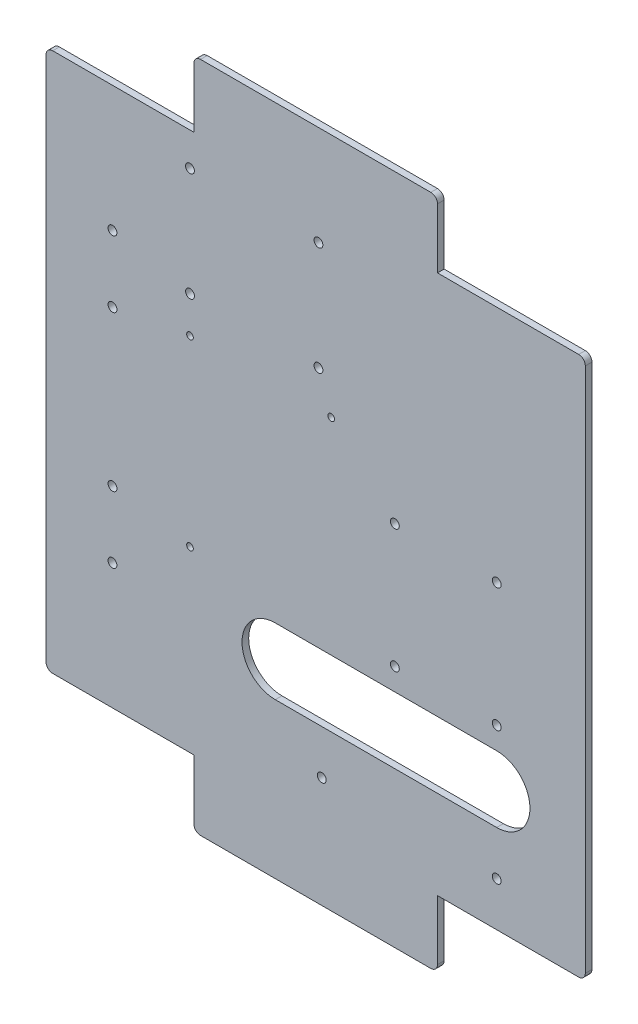
SolidWorks part; units mm, degrees
material "Alliage 1060"
ref_plane "Plan de dessus" through (0, 0, 0) normal (0, 0, 1) x (1, 0, 0)
ref_plane "Plan de droite" through (0, 0, 0) normal (0, 1, 0) x (1, 0, 0)
ref_plane "Plan de face" through (0, 0, 0) normal (1, 0, 0) x (0, 0, -1)
sketch "Esquisse1" plane through (0, 0, 0) normal (0, 0, 1) x (1, 0, 0)
  line L0 (0, 0) -> (-200, 0)
  line L1 (-200, 0) -> (-224.7487, 24.7487)
  line L2 (-224.7487, 24.7487) -> (-224.7487, 284.7487)
  line L3 (-224.7487, 284.7487) -> (-200, 309.4975)
  line L4 (-200, 309.4975) -> (0, 309.4975)
  line L5 (0, 309.4975) -> (24.7487, 284.7487)
  line L6 (24.7487, 284.7487) -> (24.7487, 24.7487)
  line L7 (24.7487, 24.7487) -> (0, 0)
  dimension "D1" = 260
  dimension "D2" = 35
  dimension "D3" = 135
  dimension "D4" = 200
extrude "Base" add sketch "Esquisse1" along normal blind 3
fillet "Congé1" radius 3 8 edges at (-200, 0, 1.5) (-224.7487, 24.7487, 1.5) (-224.7487, 284.7487, 1.5) (-200, 309.4975, 1.5) (0, 309.4975, 1.5) (24.7487, 284.7487, 1.5) (24.7487, 24.7487, 1.5) (0, 0, 1.5)
sketch "Esquisse19" plane through (0, 0, 0) normal (0, 0, -1) x (-1, 0, 0)
  line L0 (100, 309.4975) -> (100, 0) construction
  line L1 (1.2426, 309.4975) -> (198.7574, 309.4975) construction
  line L2 (198.7574, 0) -> (1.2426, 0) construction
  line L3 (-24.7487, 154.7487) -> (224.7487, 154.7487) construction
  line L4 (-24.7487, 25.9914) -> (-24.7487, 283.5061) construction
  line L5 (224.7487, 283.5061) -> (224.7487, 25.9914) construction
sketch "Esquisse25" plane through (0, 0, 0) normal (0, 0, -1) x (-1, 0, 0)
  line L0 (-24.7487, 25.9914) -> (-24.7487, 283.5061) construction
  line L1 (-21.7487, 33) -> (45, 33)
  line L2 (-24.7487, 33) -> (-24.7487, 0)
  line L3 (-24.7487, 0) -> (45, 0)
  line L4 (45, 33) -> (45, 3)
  line L5 (198.7574, 0) -> (1.2426, 0) construction
  line L6 (100, 309.4975) -> (100, 0) construction
  line L7 (100, 0) -> (100, 309.4975) construction
  line L8 (-24.7487, 154.7487) -> (224.7487, 154.7487) construction
  line L9 (224.7487, 0) -> (155, 0)
  line L10 (155, 33) -> (155, 3)
  line L11 (221.7487, 33) -> (155, 33)
  line L12 (224.7487, 33) -> (224.7487, 0)
  line L13 (224.7487, 276.4975) -> (224.7487, 309.4975)
  line L14 (221.7487, 276.4975) -> (155, 276.4975)
  line L15 (155, 276.4975) -> (155, 306.4975)
  line L16 (224.7487, 309.4975) -> (155, 309.4975)
  line L17 (-24.7487, 309.4975) -> (45, 309.4975)
  line L18 (45, 276.4975) -> (45, 306.4975)
  line L19 (-21.7487, 276.4975) -> (45, 276.4975)
  line L20 (-24.7487, 276.4975) -> (-24.7487, 309.4975)
  line L22 (45, 309.4975) -> (155, 309.4975)
  line L24 (45, 306.4975) -> (155, 306.4975)
  line L26 (45, 0) -> (155, 0)
  line L28 (45, 3) -> (155, 3)
  line L31 (-24.7487, 276.4975) -> (-24.7487, 33)
  line L33 (-21.7487, 276.4975) -> (-21.7487, 33)
  line L35 (224.7487, 276.4975) -> (224.7487, 33)
  line L37 (221.7487, 276.4975) -> (221.7487, 33)
  dimension "D1" = 55
  dimension "D2" = 33
  dimension "D3" = 3
  dimension "D4" = 3
  dimension "D5" = 3
  dimension "D6" = 3
extrude "Enlèv. mat.-Extru.1" cut sketch "Esquisse25" against normal through all
fillet "Congé2" radius 3 8 edges at (21.7487, 33, 1.5) (-45, 3, 1.5) (21.7487, 276.4975, 1.5) (-45, 306.4975, 1.5) (-155, 306.4975, 1.5) (-221.7487, 276.4975, 1.5) (-221.7487, 33, 1.5) (-155, 3, 1.5)
sketch "Esquisse26" plane through (0, 0, 0) normal (0, 0, -1) x (-1, 0, 0)
  line L0 (191.7487, 189.7487) -> (191.7487, 219.7487) construction
  line L1 (221.7487, 36) -> (221.7487, 273.4975) construction
  line L2 (-24.7487, 154.7487) -> (224.7487, 154.7487) construction
  line L3 (224.7487, 154.7487) -> (-24.7487, 154.7487) construction
  line L4 (100, 309.4975) -> (100, 0) construction
  circle A0 centre (191.7487, 189.7487) radius 2
  circle A1 centre (191.7487, 219.7487) radius 2
  circle A2 centre (191.7487, 89.7487) radius 2
  circle A3 centre (191.7487, 119.7487) radius 2
  point P8 (191.7487, 204.7487)
  dimension "D1" = 4
  dimension "D2" = 30
  dimension "D3" = 30
  dimension "D4" = 50
extrude "Enlèv. mat.-Extru.2" cut sketch "Esquisse26" against normal through all
sketch "Esquisse27" plane through (0, 0, 0) normal (0, 0, -1) x (-1, 0, 0)
  line L0 (97.2513, 53) -> (18.2513, 53) construction
  line L1 (-21.7487, 273.4975) -> (-21.7487, 36) construction
  line L2 (-18.7487, 33) -> (45, 33) construction
  circle A0 centre (97.2513, 53) radius 2
  circle A1 centre (18.2513, 53) radius 2
  dimension "D2" = 4
  dimension "D1" = 79
  dimension "D3" = 40
  dimension "D4" = 20
extrude "Enlèv. mat.-Extru.3" cut sketch "Esquisse27" against normal through all
sketch "Esquisse28" plane through (0, 0, 0) normal (0, 0, -1) x (-1, 0, 0)
  line L0 (156.7487, 113.5112) -> (156.7487, 195.9862) construction
  line L1 (156.7487, 195.9862) -> (92.9987, 195.9862) construction
  line L2 (224.7487, 154.7487) -> (-24.7487, 154.7487) construction
  line L3 (221.7487, 36) -> (221.7487, 273.4975) construction
  circle A0 centre (156.7487, 195.9862) radius 1.5
  circle A1 centre (92.9987, 195.9862) radius 1.5
  circle A2 centre (156.7487, 113.5112) radius 1.5
  point P10 (156.7487, 154.7487)
  dimension "D1" = 3
  dimension "D2" = 63.75
  dimension "D3" = 82.475
  dimension "D4" = 65
extrude "Enlèv. mat.-Extru.4" cut sketch "Esquisse28" against normal through all
sketch "Esquisse29" plane through (0, 0, 0) normal (0, 0, -1) x (-1, 0, 0)
  line L0 (221.7487, 36) -> (221.7487, 273.4975) construction
  line L1 (156.7487, 212.4975) -> (98.7487, 212.4975) construction
  line L2 (156.7487, 212.4975) -> (156.7487, 261.4975) construction
  line L3 (156.7487, 261.4975) -> (98.7487, 261.4975) construction
  line L4 (98.7487, 212.4975) -> (98.7487, 261.4975) construction
  line L5 (218.7487, 276.4975) -> (155, 276.4975) construction
  circle A0 centre (156.7487, 212.4975) radius 2
  circle A1 centre (98.7487, 212.4975) radius 2
  circle A2 centre (98.7487, 261.4975) radius 2
  circle A3 centre (156.7487, 261.4975) radius 2
  dimension "D3" = 4
  dimension "D1" = 49
  dimension "D2" = 58
  dimension "D4" = 65
  dimension "D5" = 15
extrude "Enlèv. mat.-Extru.5" cut sketch "Esquisse29" against normal through all
sketch "Esquisse30" plane through (0, 0, 0) normal (0, 0, -1) x (-1, 0, 0)
  line L0 (-21.7487, 273.4975) -> (-21.7487, 36) construction
  line L1 (64.2513, 113) -> (18.2513, 113) construction
  line L2 (64.2513, 113) -> (64.2513, 168.8) construction
  line L3 (64.2513, 168.8) -> (18.2513, 168.8) construction
  line L4 (18.2513, 113) -> (18.2513, 168.8) construction
  line L5 (-18.7487, 33) -> (45, 33) construction
  circle A0 centre (64.2513, 113) radius 2
  circle A1 centre (18.2513, 113) radius 2
  circle A2 centre (18.2513, 168.8) radius 2
  circle A3 centre (64.2513, 168.8) radius 2
  dimension "D3" = 4
  dimension "D1" = 55.8
  dimension "D2" = 46
  dimension "D4" = 40
  dimension "D5" = 80
extrude "Enlèv. mat.-Extru.6" cut sketch "Esquisse30" against normal through all
sketch "Esquisse31" plane through (0, 0, 0) normal (0, 0, -1) x (-1, 0, 0)
  line L0 (118.2513, 88) -> (18.2513, 88) construction
  line L1 (118.2513, 73) -> (18.2513, 73)
  line L2 (118.2513, 103) -> (18.2513, 103)
  line L3 (-18.7487, 33) -> (45, 33) construction
  line L4 (-21.7487, 273.4975) -> (-21.7487, 36) construction
  arc A0 (118.2513, 73) -> (118.2513, 103) centre (118.2513, 88) ccw
  arc A1 (18.2513, 103) -> (18.2513, 73) centre (18.2513, 88) ccw
  point P2 (68.2513, 88)
  dimension "D2" = 15
  dimension "D1" = 100
  dimension "D3" = 55
  dimension "D4" = 40
extrude "Enlèv. mat.-Extru.7" cut sketch "Esquisse31" against normal through all
